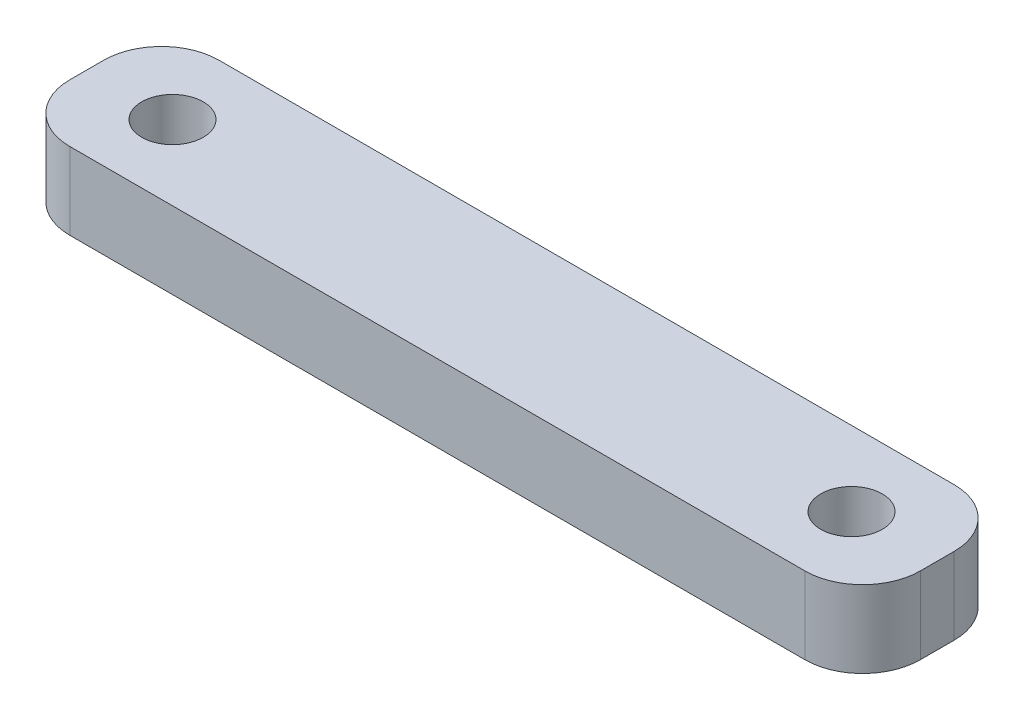
SolidWorks part; units mm, degrees
ref_plane "前视基准面" through (0, 0, 0) normal (0, 0, 1) x (1, 0, 0)
ref_plane "上视基准面" through (0, 0, 0) normal (0, 1, 0) x (1, 0, 0)
ref_plane "右视基准面" through (0, 0, 0) normal (1, 0, 0) x (0, 0, -1)
sketch "草图1" plane through (0, 0, 0) normal (0, 1, 0) x (1, 0, 0)
  line L0 (0, 0) -> (0, 49.5273) construction
  line L1 (22.1089, -3.8813) -> (-22.1089, -3.8813)
  line L2 (22.1089, -3.8813) -> (22.1089, 3.8813)
  line L3 (22.1089, 3.8813) -> (-22.1089, 3.8813)
  line L4 (-22.1089, -3.8813) -> (-22.1089, 3.8813)
  line L5 (22.1089, -3.8813) -> (-22.1089, 3.8813) construction
  line L6 (22.1089, 3.8813) -> (-22.1089, -3.8813) construction
  circle A0 centre (-17.65, 0) radius 1.6
  circle A1 centre (17.65, 0) radius 1.6
  point P0 (0, 0)
extrude "凸台-拉伸1" add sketch "草图1" along normal blind 4
fillet "圆角1" radius 3 4 edges at (-22.1089, 2, -3.8813) (22.1089, 2, -3.8813) (22.1089, 2, 3.8813) (-22.1089, 2, 3.8813)
